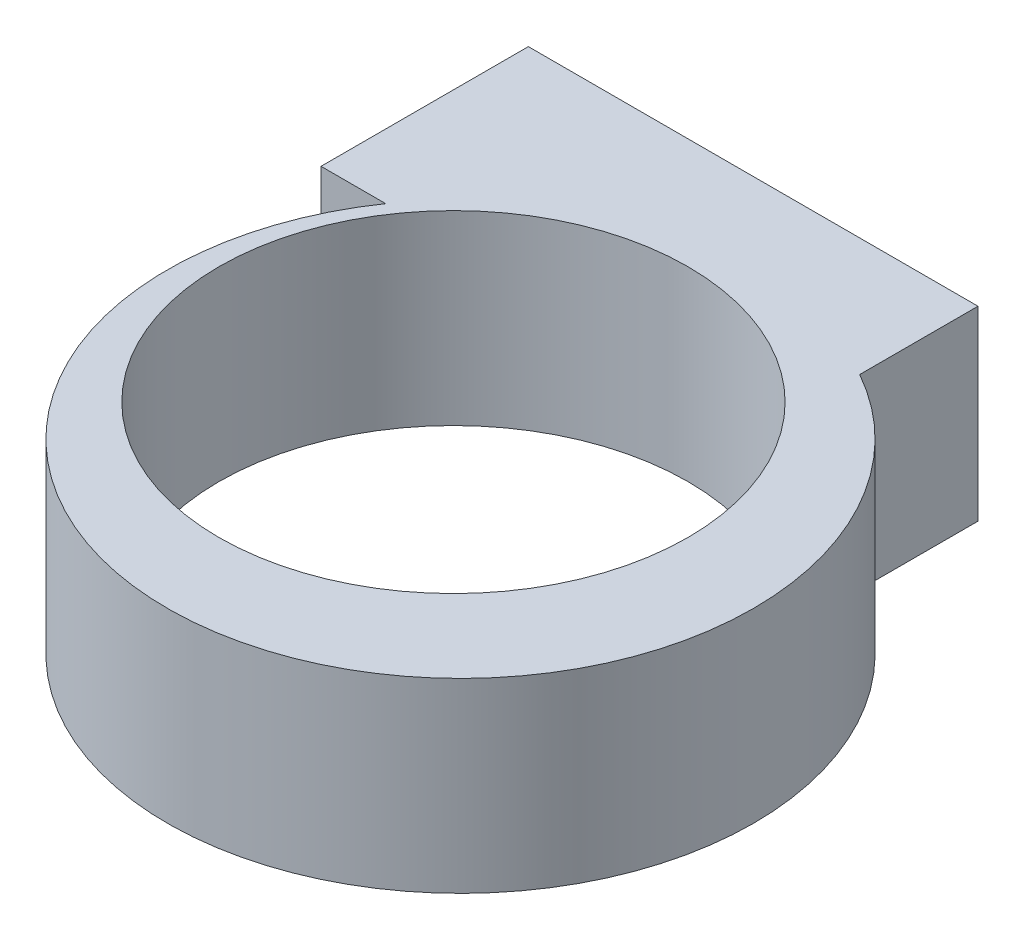
SolidWorks part; units mm, degrees
ref_plane "Front Plane" through (0, 0, 0) normal (0, 0, 1) x (1, 0, 0)
ref_plane "Top Plane" through (0, 0, 0) normal (0, 1, 0) x (1, 0, 0)
ref_plane "Right Plane" through (0, 0, 0) normal (1, 0, 0) x (0, 0, -1)
sketch "Sketch1" plane through (0, 0, 0) normal (0, 1, 0) x (1, 0, 0)
  circle A0 centre (0, 0) radius 5
extrude "Boss-Extrude1" add sketch "Sketch1" along normal blind 3.175 contours A0
sketch "Sketch2" plane through (0, 3.175, 0) normal (0, 1, 0) x (1, 0, 0)
  line L1 (-5.2183, 2.8398) -> (2.4508, 2.8398)
  line L2 (-5.2183, 2.8398) -> (-5.2183, 6.3757)
  line L3 (-5.2183, 6.3757) -> (2.4508, 6.3757)
  line L4 (2.4508, 2.8398) -> (2.4508, 6.3757)
extrude "Boss-Extrude2" add sketch "Sketch2" against normal up to surface (3.175 mm away) up to face at (0, 0, 5)
hole_wizard "Ø8.0 (8) Diameter Hole1" positions "Sketch3" profile "Sketch4" hole size "Ø8.0" standard "ANSI Metric" end condition through all
sketch "Sketch3" plane through (0, 3.175, 0) normal (0, 1, 0) x (1, 0, 0)
  point P0 (-0.6065, 0.4866)
sketch "Sketch4" plane through (-0.6065, 3.175, -0.4866) normal (1, 0, 0) x (0, 0, 1)
  line L0 (0, 0) -> (0, 3.175)
  line L1 (0, 3.175) -> (4, 3.175)
  line L2 (4, 3.175) -> (4, 0)
  line L5 (4, 0) -> (0, 0)
  line L11 (0, -6.35) -> (0, 107.95) construction
  dimension "Thru Hole Dia." = 8
  dimension "Thru Hole Depth" = 3.175
